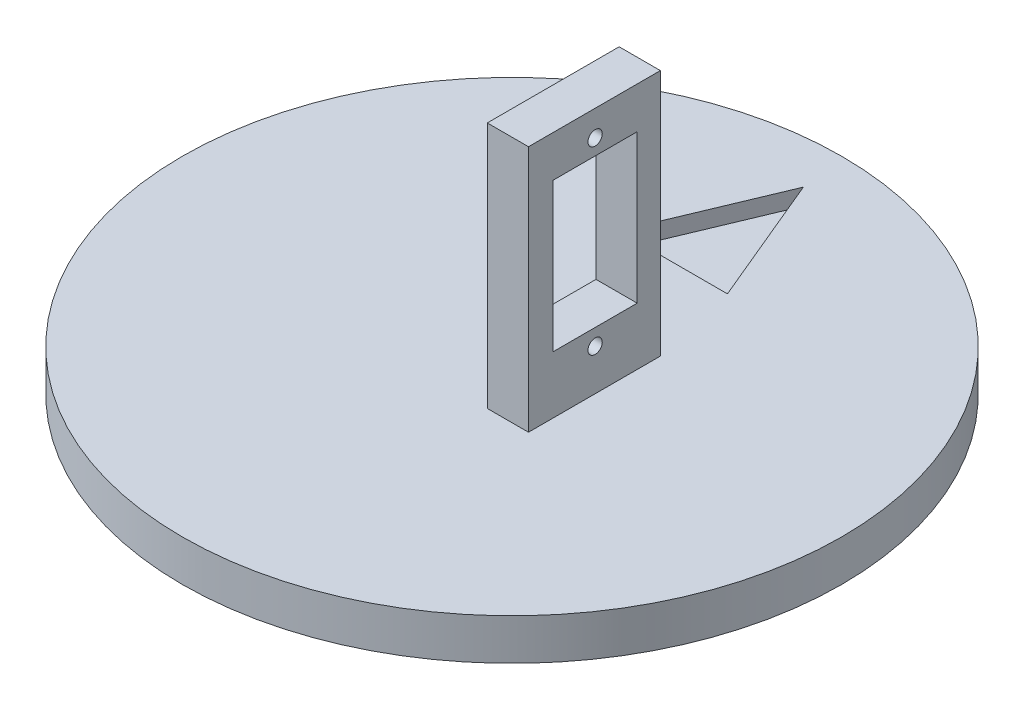
SolidWorks part; units mm, degrees
ref_plane "Front Plane" through (0, 0, 0) normal (0, 0, 1) x (1, 0, 0)
ref_plane "Top Plane" through (0, 0, 0) normal (0, 1, 0) x (1, 0, 0)
ref_plane "Right Plane" through (0, 0, 0) normal (1, 0, 0) x (0, 0, -1)
sketch "Sketch1" plane through (0, 0, 0) normal (0, 1, 0) x (1, 0, 0)
  circle A0 centre (0, 0) radius 50.8
  dimension "D1" = 101.6
extrude "Boss-Extrude1" add sketch "Sketch1" along normal blind 6.35
sketch "Sketch2" plane through (0, 6.35, 0) normal (0, 1, 0) x (1, 0, 0)
  line L1 (12.7, 10.16) -> (6.35, 10.16)
  line L2 (12.7, 10.16) -> (12.7, -10.16)
  line L3 (12.7, -10.16) -> (6.35, -10.16)
  line L4 (6.35, 10.16) -> (6.35, -10.16)
  dimension "D1" = 20.32
  dimension "D2" = 6.35
  dimension "D3" = 10.16
  dimension "D4" = 6.35
extrude "Boss-Extrude2" add sketch "Sketch2" along normal blind 38.1 contours L1 L4 L3 L2
extrude "Cut-Extrude1" cut sketch "Sketch3" against normal blind 12.7
sketch "Sketch3" plane through (6.35, 55.2468, 64.643) normal (-1, 0, 0) x (0, 0, 1)
  line L1 (-71.2329, -17.1674) -> (-58.293, -17.1674)
  line L2 (-71.2329, -17.1674) -> (-71.2329, -40.0491)
  line L3 (-71.2329, -40.0491) -> (-58.293, -40.0491)
  line L4 (-58.293, -17.1674) -> (-58.293, -40.0491)
  circle A0 centre (-64.7503, -14.7468) radius 1.1
  circle A1 centre (-64.7503, -42.5468) radius 1.1
sketch "Sketch4" plane through (0, 6.35, 0) normal (0, 1, 0) x (1, 0, 0)
  line L0 (-7.231, 23.6341) -> (9.5604, 23.6341)
  line L1 (9.5604, 23.6341) -> (1.1647, 43.7256)
  line L2 (1.1647, 43.7256) -> (-7.231, 23.6341)
extrude "Cut-Extrude2" cut sketch "Sketch4" against normal blind 2.54
